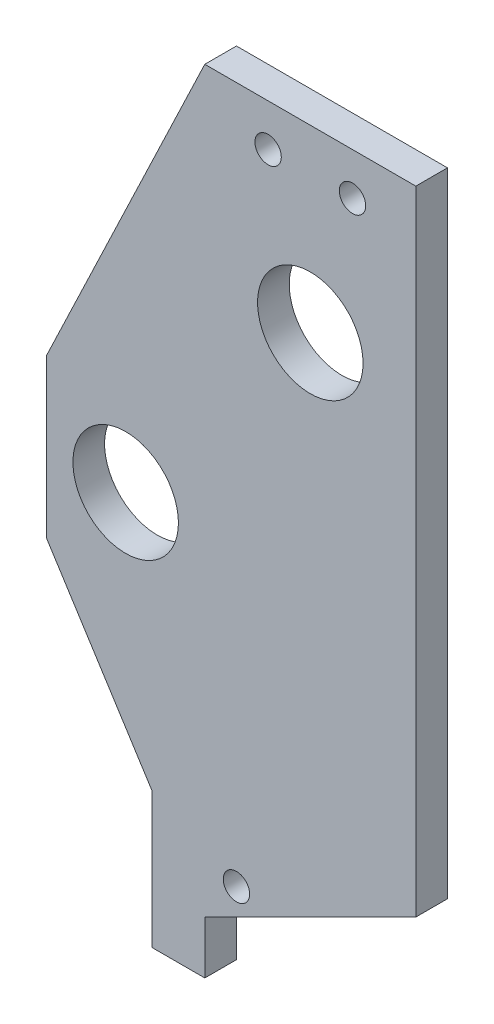
SolidWorks part; units mm, degrees
ref_plane "Front Plane" through (0, 0, 0) normal (0, 0, 1) x (1, 0, 0)
ref_plane "Top Plane" through (0, 0, 0) normal (0, 1, 0) x (1, 0, 0)
ref_plane "Right Plane" through (0, 0, 0) normal (1, 0, 0) x (0, 0, -1)
sketch "Sketch1" plane through (0, 0, 0) normal (0, 0, 1) x (1, 0, 0)
  line L1 (-16.2048, 29.823) -> (3.7952, 29.823)
  line L2 (-16.2048, 29.823) -> (-16.2048, -40.177)
  line L3 (-16.2048, -40.177) -> (3.7952, -40.177)
  line L4 (3.7952, 29.823) -> (3.7952, -40.177)
  dimension "D1" = 70
  dimension "D2" = 20
extrude "Boss-Extrude1" add sketch "Sketch1" along normal blind 3
sketch "Sketch2" plane through (0, 0, 3) normal (0, 0, 1) x (1, 0, 0)
  line L0 (-16.2048, 29.823) -> (-16.2048, -40.177) construction
  line L1 (-16.2048, -16.577) -> (-31.2048, -16.577)
  line L2 (-16.2048, -16.577) -> (-16.2048, -1.577)
  line L3 (-16.2048, -1.577) -> (-31.2048, -1.577)
  line L4 (-31.2048, -16.577) -> (-31.2048, -1.577)
  dimension "D1" = 23.6
  dimension "D2" = 15
  dimension "D3" = 15
extrude "Boss-Extrude2" add sketch "Sketch2" against normal blind 3
sketch "Sketch3" plane through (0, 0, 3) normal (0, 0, 1) x (1, 0, 0)
  line L0 (-31.2048, -1.577) -> (-16.2048, 29.823)
  line L1 (-16.2048, 29.823) -> (-16.2048, -1.577)
  line L2 (-16.2048, -1.577) -> (-31.2048, -1.577)
  line L3 (-31.2048, -16.577) -> (-16.2048, -16.577)
  line L4 (-16.2048, -16.577) -> (-16.2048, -40.177)
  line L5 (-16.2048, -40.177) -> (-31.2048, -16.577)
extrude "Boss-Extrude3" add sketch "Sketch3" against normal blind 3
sketch "Sketch6" plane through (0, 0, 3) normal (0, 0, 1) x (1, 0, 0)
  line L0 (-16.2048, -40.177) -> (-16.2048, -45.177)
  line L1 (-16.2048, -45.177) -> (-21.2048, -45.177)
  line L2 (-21.2048, -45.177) -> (-21.2048, -32.3104)
  line L3 (-31.2048, -16.577) -> (-16.2048, -40.177) construction
  line L4 (-16.2048, -40.177) -> (-21.2048, -32.3104)
extrude "Boss-Extrude4" add sketch "Sketch6" against normal blind 3
sketch "Sketch7" plane through (0, 0, 3) normal (0, 0, 1) x (1, 0, 0)
  line L0 (3.7952, -40.177) -> (3.7952, -30.177)
  line L1 (3.7952, -40.177) -> (3.7952, 29.823) construction
  line L2 (3.7952, -30.177) -> (-16.2048, -40.177)
  line L3 (-16.2048, -40.177) -> (3.7952, -40.177)
  line L4 (-31.2048, -1.577) -> (-31.2048, -16.577) construction
  line L5 (3.7952, 29.823) -> (-16.2048, 29.823) construction
  circle A0 centre (-23.7048, -9.077) radius 5
  circle A1 centre (-13.2048, -36.177) radius 1.25
  circle A2 centre (-6.2048, 12.7805) radius 5
  circle A3 centre (-10.2048, 25.823) radius 1.25
  circle A4 centre (-2.2048, 25.823) radius 1.25
  dimension "D1" = 7.5
  dimension "D3" = 3
  dimension "D5" = 10
  dimension "D7" = 6
  dimension "D2" = 7.5
  dimension "D4" = 4
  dimension "D6" = 28
  dimension "D8" = 6
  dimension "D9" = 4
  dimension "D10" = 4
extrude "Cut-Extrude1" cut sketch "Sketch7" against normal through all
